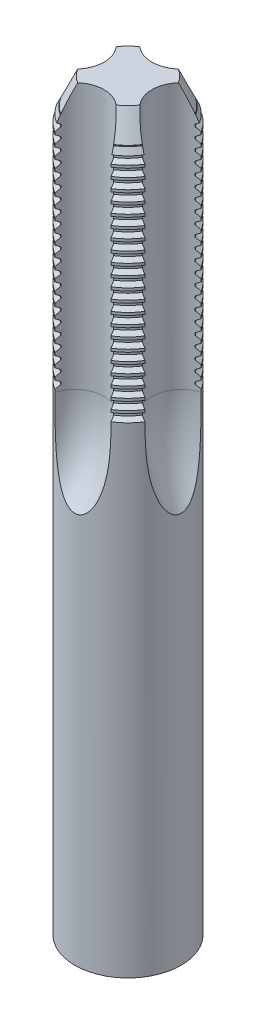
SolidWorks part; units mm, degrees
ref_plane "前视基准面" through (0, 0, 0) normal (0, 0, 1) x (1, 0, 0)
ref_plane "上视基准面" through (0, 0, 0) normal (0, 1, 0) x (1, 0, 0)
ref_plane "右视基准面" through (0, 0, 0) normal (1, 0, 0) x (0, 0, -1)
sketch "草图1" plane through (0, 0, 0) normal (0, 0, 1) x (1, 0, 0)
  line L0 (0, 64.7163) -> (0, -50.404) construction
  line L1 (0, 60) -> (0, -80)
  line L2 (0, 60) -> (10, 60)
  line L4 (0, -80) -> (10, -80)
  line L5 (10, 60) -> (10, -80)
  line L6 (0, 0) -> (10, -80) construction
  line L7 (0, 0) -> (10, 60) construction
  point P3 (0, 0)
  dimension "D1" = 140
revolve "旋转1" add sketch "草图1" angle 360 about L0
sketch "草图2" plane through (0, 60, 0) normal (0, 1, 0) x (1, 0, 0)
  circle A0 centre (0, 0) radius 10
sketch "草图3" plane through (0, 60, 0) normal (0, 1, 0) x (1, 0, 0)
  arc A0 (-9, 5.4083) -> (-9, -5.4083) centre (0, 0) ccw
  circle A1 centre (0, 0) radius 10 construction
  arc A7 (-9, 5.4083) -> (-9, -5.4083) centre (-10, 0) cw
  dimension "D1" = 21
sketch "草图6" plane through (0, 0, 0) normal (0, 0, 1) x (1, 0, 0)
  line L0 (-6.75, 60) -> (-6.75, 10)
  line L1 (-4.5, 60) -> (-9, 60) construction
  arc A0 (-6.75, 10) -> (-13.0195, -6.4369) centre (-31.4314, 10) cw
  dimension "D1" = 50
sweep "切除-扫描3" cut profiles "草图3" path "草图6"
pattern_circular "阵列(圆周)2" count 4 over 360 about axis through (0, 0, 0) along (0, 1, 0) of "切除-扫描3"
sketch "草图8" plane through (0, 0, 0) normal (0, 0, 1) x (1, 0, 0)
  line L0 (-5.2879, 60) -> (-11.8438, 60) construction
  line L1 (-10, 60) -> (-9.1503, 59.4727)
  line L2 (-10, 10) -> (-10, 60) construction
  line L3 (-9.1503, 59.4727) -> (-9.1503, 59.0273)
  line L4 (-9.1503, 59.0273) -> (-10, 58.5)
  line L5 (-10, 58.5) -> (-10, 60)
  line L6 (-10, 58) -> (-9.1503, 57.4727)
  line L7 (-9.1503, 57.0273) -> (-10, 56.5)
  line L8 (-9.1503, 57.4727) -> (-9.1503, 57.0273)
  line L9 (-10, 56.5) -> (-10, 58)
  line L10 (-10, 56) -> (-9.1503, 55.4727)
  line L11 (-9.1503, 55.0273) -> (-10, 54.5)
  line L12 (-9.1503, 55.4727) -> (-9.1503, 55.0273)
  line L13 (-10, 54.5) -> (-10, 56)
  line L14 (-10, 54) -> (-9.1503, 53.4727)
  line L15 (-9.1503, 53.0273) -> (-10, 52.5)
  line L16 (-9.1503, 53.4727) -> (-9.1503, 53.0273)
  line L17 (-10, 52.5) -> (-10, 54)
  line L18 (-10, 52) -> (-9.1503, 51.4727)
  line L19 (-9.1503, 51.0273) -> (-10, 50.5)
  line L20 (-9.1503, 51.4727) -> (-9.1503, 51.0273)
  line L21 (-10, 50.5) -> (-10, 52)
  line L22 (-10, 50) -> (-9.1503, 49.4727)
  line L23 (-9.1503, 49.0273) -> (-10, 48.5)
  line L24 (-9.1503, 49.4727) -> (-9.1503, 49.0273)
  line L25 (-10, 48.5) -> (-10, 50)
  line L26 (-10, 48) -> (-9.1503, 47.4727)
  line L27 (-9.1503, 47.0273) -> (-10, 46.5)
  line L28 (-9.1503, 47.4727) -> (-9.1503, 47.0273)
  line L29 (-10, 46.5) -> (-10, 48)
  line L30 (-10, 46) -> (-9.1503, 45.4727)
  line L31 (-9.1503, 45.0273) -> (-10, 44.5)
  line L32 (-9.1503, 45.4727) -> (-9.1503, 45.0273)
  line L33 (-10, 44.5) -> (-10, 46)
  line L34 (-10, 44) -> (-9.1503, 43.4727)
  line L35 (-9.1503, 43.0273) -> (-10, 42.5)
  line L36 (-9.1503, 43.4727) -> (-9.1503, 43.0273)
  line L37 (-10, 42.5) -> (-10, 44)
  line L38 (-10, 42) -> (-9.1503, 41.4727)
  line L39 (-9.1503, 41.0273) -> (-10, 40.5)
  line L40 (-9.1503, 41.4727) -> (-9.1503, 41.0273)
  line L41 (-10, 40.5) -> (-10, 42)
  line L42 (-10, 40) -> (-9.1503, 39.4727)
  line L43 (-9.1503, 39.0273) -> (-10, 38.5)
  line L44 (-9.1503, 39.4727) -> (-9.1503, 39.0273)
  line L45 (-10, 38.5) -> (-10, 40)
  line L46 (-10, 38) -> (-9.1503, 37.4727)
  line L47 (-9.1503, 37.0273) -> (-10, 36.5)
  line L48 (-9.1503, 37.4727) -> (-9.1503, 37.0273)
  line L49 (-10, 36.5) -> (-10, 38)
  line L50 (-10, 36) -> (-9.1503, 35.4727)
  line L51 (-9.1503, 35.0273) -> (-10, 34.5)
  line L52 (-9.1503, 35.4727) -> (-9.1503, 35.0273)
  line L53 (-10, 34.5) -> (-10, 36)
  line L54 (-10, 34) -> (-9.1503, 33.4727)
  line L55 (-9.1503, 33.0273) -> (-10, 32.5)
  line L56 (-9.1503, 33.4727) -> (-9.1503, 33.0273)
  line L57 (-10, 32.5) -> (-10, 34)
  line L58 (-10, 32) -> (-9.1503, 31.4727)
  line L59 (-9.1503, 31.0273) -> (-10, 30.5)
  line L60 (-9.1503, 31.4727) -> (-9.1503, 31.0273)
  line L61 (-10, 30.5) -> (-10, 32)
  line L62 (-10, 30) -> (-9.1503, 29.4727)
  line L63 (-9.1503, 29.0273) -> (-10, 28.5)
  line L64 (-9.1503, 29.4727) -> (-9.1503, 29.0273)
  line L65 (-10, 28.5) -> (-10, 30)
  line L66 (-10, 28) -> (-9.1503, 27.4727)
  line L67 (-9.1503, 27.0273) -> (-10, 26.5)
  line L68 (-9.1503, 27.4727) -> (-9.1503, 27.0273)
  line L69 (-10, 26.5) -> (-10, 28)
  line L70 (-10, 26) -> (-9.1503, 25.4727)
  line L71 (-9.1503, 25.0273) -> (-10, 24.5)
  line L72 (-9.1503, 25.4727) -> (-9.1503, 25.0273)
  line L73 (-10, 24.5) -> (-10, 26)
  line L74 (-10, 24) -> (-9.1503, 23.4727)
  line L75 (-9.1503, 23.0273) -> (-10, 22.5)
  line L76 (-9.1503, 23.4727) -> (-9.1503, 23.0273)
  line L77 (-10, 22.5) -> (-10, 24)
  line L78 (-10, 22) -> (-9.1503, 21.4727)
  line L79 (-9.1503, 21.0273) -> (-10, 20.5)
  line L80 (-9.1503, 21.4727) -> (-9.1503, 21.0273)
  line L81 (-10, 20.5) -> (-10, 22)
  line L82 (-10, 20) -> (-9.1503, 19.4727)
  line L83 (-9.1503, 19.0273) -> (-10, 18.5)
  line L84 (-9.1503, 19.4727) -> (-9.1503, 19.0273)
  line L85 (-10, 18.5) -> (-10, 20)
  line L86 (-10, 18) -> (-9.1503, 17.4727)
  line L87 (-9.1503, 17.0273) -> (-10, 16.5)
  line L88 (-9.1503, 17.4727) -> (-9.1503, 17.0273)
  line L89 (-10, 16.5) -> (-10, 18)
  line L90 (-10, 16) -> (-9.1503, 15.4727)
  line L91 (-9.1503, 15.0273) -> (-10, 14.5)
  line L92 (-9.1503, 15.4727) -> (-9.1503, 15.0273)
  line L93 (-10, 14.5) -> (-10, 16)
  line L94 (-10, 14) -> (-9.1503, 13.4727)
  line L95 (-9.1503, 13.0273) -> (-10, 12.5)
  line L96 (-9.1503, 13.4727) -> (-9.1503, 13.0273)
  line L97 (-10, 12.5) -> (-10, 14)
  line L98 (-10, 12) -> (-9.1503, 11.4727)
  line L99 (-9.1503, 11.0273) -> (-10, 10.5)
  line L100 (-9.1503, 11.4727) -> (-9.1503, 11.0273)
  line L101 (-10, 10.5) -> (-10, 12)
  line L102 (-10, 60) -> (-10, 58) construction
  dimension "D1" = 1.5
  dimension "D2" = 1
  dimension "D3" = 2
revolve "切除-旋转5" cut sketch "草图8" angle 360 about axis through (0, 64.7163, 0) along (0, 1, 0)
sketch "草图10" plane through (0, 0, 0) normal (0, 0, 1) x (1, 0, 0)
  line L0 (-10, 53.3091) -> (-6.8877, 60)
  line L1 (-10, 10) -> (-10, 60) construction
  line L2 (-5.2879, 60) -> (-8.4875, 60) construction
  line L3 (-6.8877, 60) -> (-10, 60)
  line L4 (-10, 60) -> (-10, 53.3091)
  line L5 (0, 60) -> (0, 41.4469) construction
  line L6 (0, 10) -> (0, 60) construction
revolve "切除-旋转7" cut sketch "草图10" angle 360 about L5
